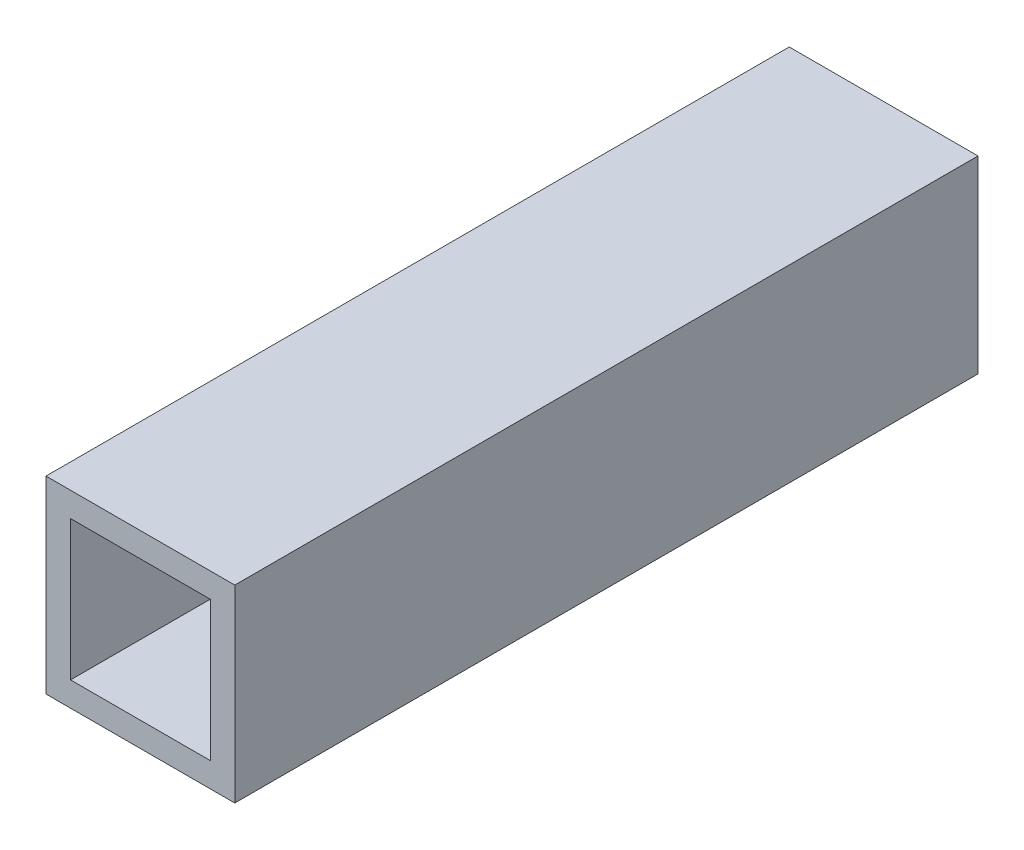
SolidWorks part; units mm, degrees
ref_plane "Front Plane" through (0, 0, 0) normal (0, 0, 1) x (1, 0, 0)
ref_plane "Top Plane" through (0, 0, 0) normal (0, 1, 0) x (1, 0, 0)
ref_plane "Right Plane" through (0, 0, 0) normal (1, 0, 0) x (0, 0, -1)
sketch "Sketch1" plane through (0, 0, 0) normal (0, 0, 1) x (1, 0, 0)
  line L1 (6.35, 6.35) -> (-6.35, 6.35)
  line L2 (6.35, 6.35) -> (6.35, -6.35)
  line L3 (6.35, -6.35) -> (-6.35, -6.35)
  line L4 (-6.35, 6.35) -> (-6.35, -6.35)
  line L5 (6.35, 6.35) -> (-6.35, -6.35) construction
  line L6 (6.35, -6.35) -> (-6.35, 6.35) construction
  line L7 (4.7, 4.7) -> (-4.7, 4.7)
  line L8 (4.7, 4.7) -> (4.7, -4.7)
  line L9 (4.7, -4.7) -> (-4.7, -4.7)
  line L10 (-4.7, 4.7) -> (-4.7, -4.7)
  line L11 (4.7, 4.7) -> (-4.7, -4.7) construction
  line L12 (4.7, -4.7) -> (-4.7, 4.7) construction
  point P0 (0, 0)
  point P5 (0, 0)
  dimension "D1" = 12.7
  dimension "D2" = 9.4
extrude "Boss-Extrude1" add sketch "Sketch1" along normal blind 50
